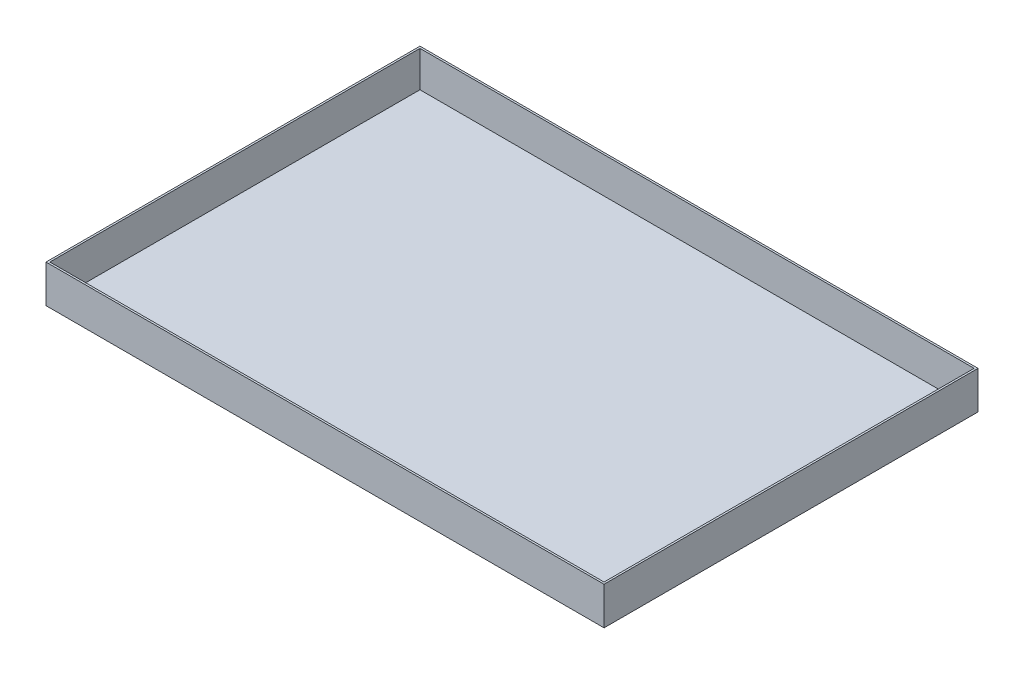
SolidWorks part; units mm, degrees
ref_plane "Front Plane" through (0, 0, 0) normal (0, 0, 1) x (1, 0, 0)
ref_plane "Top Plane" through (0, 0, 0) normal (0, 1, 0) x (1, 0, 0)
ref_plane "Right Plane" through (0, 0, 0) normal (1, 0, 0) x (0, 0, -1)
sketch "Sketch1" plane through (0, 0, 0) normal (0, 1, 0) x (1, 0, 0)
  line L1 (0, 0) -> (923.925, 0)
  line L2 (0, 0) -> (0, 619.125)
  line L3 (0, 619.125) -> (923.925, 619.125)
  line L4 (923.925, 0) -> (923.925, 619.125)
  dimension "D1" = 923.925
  dimension "D2" = 619.125
extrude "Boss-Extrude1" add sketch "Sketch1" along normal blind 3.175 contours L2 L3 L4 L1
sketch "Sketch2" plane through (0, 3.175, 0) normal (0, 1, 0) x (1, 0, 0)
  line L0 (0, 619.125) -> (923.925, 619.125) construction
  line L1 (0, 0) -> (3.175, 0)
  line L2 (0, 0) -> (0, 619.125)
  line L3 (0, 619.125) -> (3.175, 619.125)
  line L4 (3.175, 0) -> (3.175, 619.125)
  line L6 (923.925, 0) -> (920.75, 0)
  line L7 (923.925, 0) -> (923.925, 619.125)
  line L8 (923.925, 619.125) -> (920.75, 619.125)
  line L9 (920.75, 0) -> (920.75, 619.125)
  dimension "D1" = 3.175
  dimension "D2" = 3.175
extrude "Boss-Extrude2" add sketch "Sketch2" along normal blind 59.4
sketch "Sketch3" plane through (0, 3.175, 0) normal (0, 1, 0) x (1, 0, 0)
  line L0 (920.75, 619.125) -> (920.75, 0) construction
  line L1 (3.175, 0) -> (920.75, 0)
  line L2 (3.175, 0) -> (3.175, 3.175)
  line L3 (3.175, 3.175) -> (920.75, 3.175)
  line L4 (920.75, 0) -> (920.75, 3.175)
  line L5 (3.175, 0) -> (3.175, 619.125) construction
  line L6 (920.75, 619.125) -> (3.175, 619.125)
  line L7 (920.75, 619.125) -> (920.75, 615.95)
  line L8 (920.75, 615.95) -> (3.175, 615.95)
  line L9 (3.175, 619.125) -> (3.175, 615.95)
  dimension "D1" = 3.175
  dimension "D2" = 3.175
extrude "Boss-Extrude3" add sketch "Sketch3" along normal up to surface (59.4 mm away) up to face at (1.5875, 62.575, -309.5625)
